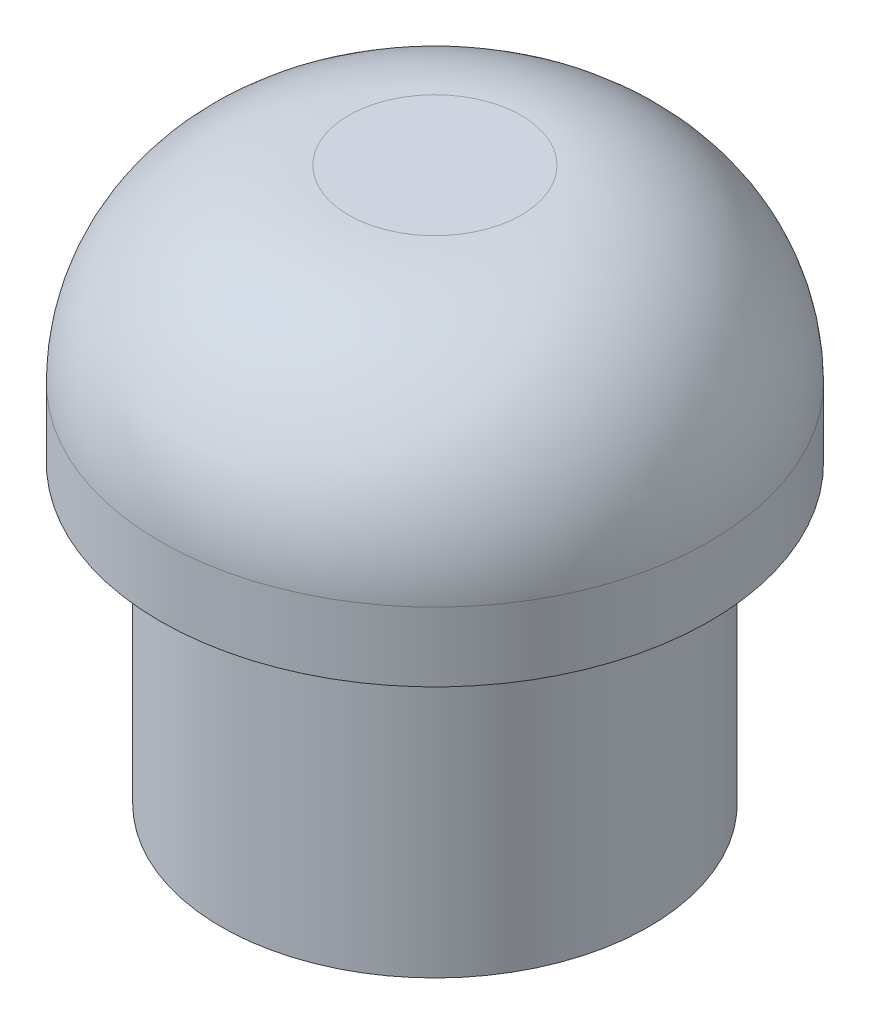
SolidWorks part; units mm, degrees
material "Black Plastic"
ref_plane "Front Plane" through (0, 0, 0) normal (0, 0, 1) x (1, 0, 0)
ref_plane "Top Plane" through (0, 0, 0) normal (0, 1, 0) x (1, 0, 0)
ref_plane "Right Plane" through (0, 0, 0) normal (1, 0, 0) x (0, 0, -1)
sketch "Sketch1" plane through (0, 0, 0) normal (0, 1, 0) x (1, 0, 0)
  circle A0 centre (0, 0) radius 8.75
extrude "Boss-Extrude1" add sketch "Sketch1" along normal blind 8.2
fillet "Fillet1" radius 6 1 edges at (0, 8.2, 8.75)
sketch "Sketch2" plane through (0, 0, 0) normal (0, -1, 0) x (1, 0, 0)
  line L1 (6.8068, 18.8968) -> (-6.8068, 18.8968)
  line L2 (6.8068, 18.8968) -> (6.8068, -5.2832)
  line L3 (6.8068, -5.2832) -> (-6.8068, -5.2832)
  line L4 (-6.8068, 18.8968) -> (-6.8068, -5.2832)
  line L5 (6.8068, 18.8968) -> (-6.8068, -5.2832) construction
  line L6 (6.8068, -5.2832) -> (-6.8068, 18.8968) construction
  circle A0 centre (0, 0) radius 6.8068
  point P3 (0, 6.8068)
  dimension "D1" = 12.09
extrude "Boss-Extrude2" add sketch "Sketch2" along normal blind 9.4 contours L3 A0
sketch "Mount Cutout" plane through (0, 0, 0) normal (0, -1, 0) x (1, 0, 0)
  circle A0 centre (0, 0) radius 6.35
  dimension "D1" = 12.7
sketch3d "3DSketch2"
  line L0 (0, -9.4, 0) -> (0, 0, 0)
  arc A0 (4.292, -9.4, -5.2832) -> (-4.292, -9.4, -5.2832) centre (0, -9.4, 0) ccw construction
  point P6 (0, -16.2068, 0)
